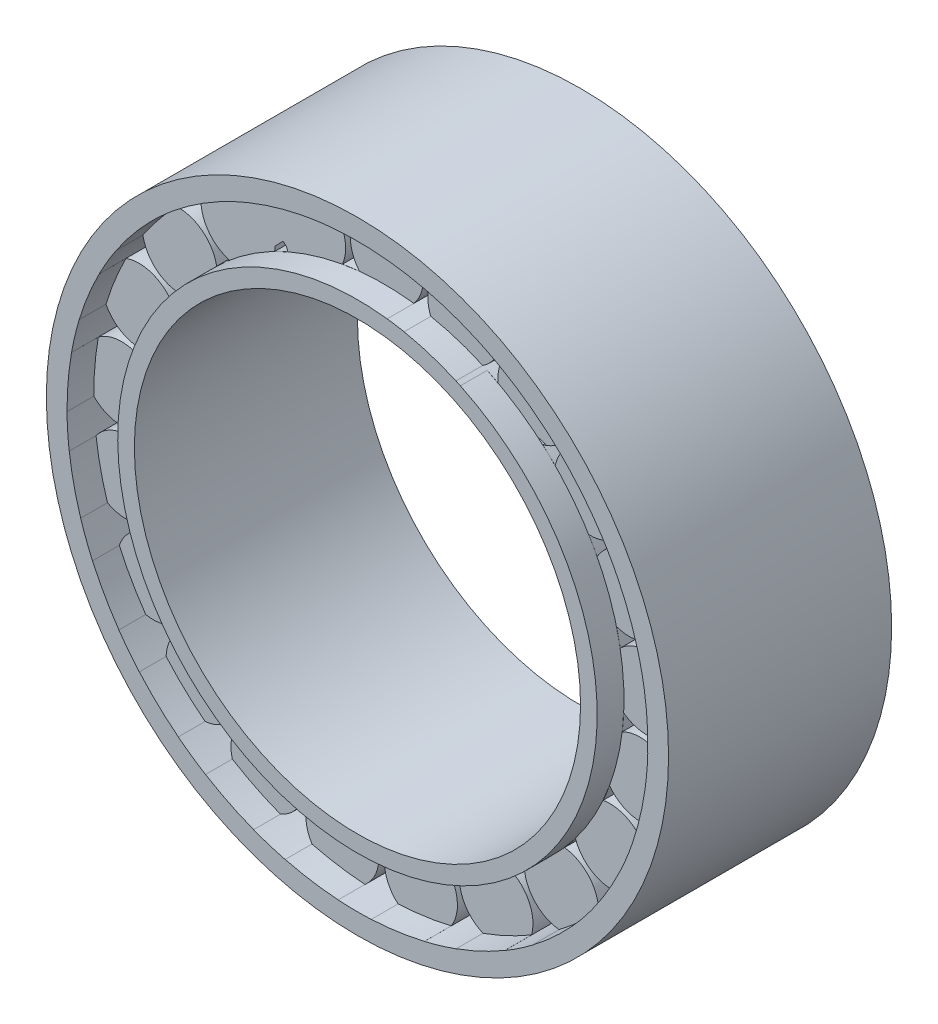
SolidWorks part; units mm, degrees
ref_plane "Front" through (0, 0, 0) normal (0, 0, 1) x (1, 0, 0)
ref_plane "Top" through (0, 0, 0) normal (0, 1, 0) x (1, 0, 0)
ref_plane "Right" through (0, 0, 0) normal (1, 0, 0) x (0, 0, -1)
sketch "Sketch1" plane through (0, 0, 0) normal (0, 0, 1) x (1, 0, 0)
  line L0 (0, 0) -> (0, 20.9407) construction
  circle A1 centre (0, 0) radius 17.7101
  circle A2 centre (0, 0) radius 12.7
  arc A3 (1.6898, 13.5424) -> (1.6754, 16.4463) centre (0, 14.986) ccw
  arc A4 (5.607, 12.4424) -> (6.4492, 15.2216) centre (4.4178, 14.32) ccw
  arc A5 (6.4823, 12.0097) -> (5.607, 12.4424) centre (0.0006, -0.0002) ccw
  arc A6 (8.1492, 14.3835) -> (6.4823, 12.0097) centre (8.694, 12.2288) ccw
  arc A7 (8.1492, 14.3835) -> (6.4492, 15.2216) centre (0.0006, -0.0002) ccw
  arc A8 (2.6538, 13.3869) -> (1.6898, 13.5424) centre (0, 0) ccw
  arc A9 (3.5469, 16.1465) -> (2.6538, 13.3869) centre (4.7026, 14.2481) ccw
  arc A10 (3.5469, 16.1465) -> (1.6754, 16.4463) centre (0, 0) ccw
  arc A11 (9.026, 10.2368) -> (10.6499, 12.6443) centre (8.443, 12.3814) ccw
  arc A12 (9.7349, 9.5653) -> (9.026, 10.2368) centre (0.0011, -0.0006) ccw
  arc A13 (12.0273, 11.3423) -> (9.7349, 9.5653) centre (11.9129, 9.1227) ccw
  arc A14 (12.0273, 11.3423) -> (10.6499, 12.6443) centre (0.0011, -0.0006) ccw
  arc A15 (11.6429, 7.1213) -> (13.9044, 8.9432) centre (11.718, 9.3425) ccw
  arc A16 (12.1224, 6.2707) -> (11.6429, 7.1213) centre (0.0015, -0.0011) ccw
  arc A17 (14.8368, 7.293) -> (12.1224, 6.2707) centre (14.0732, 5.2058) ccw
  arc A18 (14.8368, 7.293) -> (13.9044, 8.9432) centre (0.0015, -0.0011) ccw
  arc A19 (13.2253, 3.3729) -> (15.9233, 4.4473) centre (13.9518, 5.4733) ccw
  arc A20 (13.4328, 2.4188) -> (13.2253, 3.3729) centre (0.0017, -0.0017) ccw
  arc A21 (16.3279, 2.5956) -> (13.4328, 2.4188) centre (14.983, 0.8262) ccw
  arc A22 (16.3279, 2.5956) -> (15.9233, 4.4473) centre (0.0017, -0.0017) ccw
  arc A23 (13.6325, -0.6754) -> (16.5273, -0.444) centre (14.9459, 1.1176) ccw
  arc A24 (13.5495, -1.6483) -> (13.6325, -0.6754) centre (0.0018, -0.0023) ccw
  arc A25 (16.3682, -2.3326) -> (13.5495, -1.6483) centre (14.5615, -3.627) ccw
  arc A26 (16.3682, -2.3326) -> (16.5273, -0.444) centre (0.0018, -0.0023) ccw
  arc A27 (12.8284, -4.6638) -> (15.6628, -5.296) centre (14.6119, -3.3376) ccw
  arc A28 (12.4623, -5.569) -> (12.8284, -4.6638) centre (0.0016, -0.0029) ccw
  arc A29 (14.954, -7.0538) -> (12.4623, -5.569) centre (12.8461, -7.7581) ccw
  arc A30 (14.954, -7.0538) -> (15.6628, -5.296) centre (0.0016, -0.0029) ccw
  arc A31 (10.8844, -8.2381) -> (13.4065, -9.6776) centre (12.9795, -7.4965) ccw
  arc A32 (10.2678, -8.9951) -> (10.8844, -8.2381) centre (0.0013, -0.0035) ccw
  arc A33 (12.2111, -11.1484) -> (10.2678, -8.9951) centre (9.9892, -11.2001) ccw
  arc A34 (12.2111, -11.1484) -> (13.4065, -9.6776) centre (0.0013, -0.0035) ccw
  arc A35 (7.9732, -11.0805) -> (9.959, -13.1995) centre (10.1939, -10.9894) ccw
  arc A36 (7.1608, -11.6222) -> (7.9732, -11.0805) centre (0.0008, -0.0039) ccw
  arc A37 (8.3832, -14.2526) -> (7.1608, -11.6222) centre (6.2447, -13.6471) ccw
  arc A38 (8.3832, -14.2526) -> (9.959, -13.1995) centre (0.0008, -0.0039) ccw
  arc A39 (4.3536, -12.9386) -> (5.6266, -15.5487) centre (6.5024, -13.5061) ccw
  arc A40 (3.4176, -13.2167) -> (4.3536, -12.9386) centre (0.0002, -0.0042) ccw
  arc A41 (3.8103, -16.0906) -> (3.4176, -13.2167) centre (1.9453, -14.8817) ccw
  arc A42 (3.8103, -16.0906) -> (5.6266, -15.5487) centre (0.0002, -0.0042) ccw
  arc A43 (0.3471, -13.6472) -> (0.7941, -16.5166) centre (2.2331, -14.8229) ccw
  arc A44 (-0.6293, -13.6371) -> (0.3471, -13.6472) centre (-0.0004, -0.0042) ccw
  arc A45 (-1.1011, -16.499) -> (-0.6293, -13.6371) centre (-2.5269, -14.7941) ccw
  arc A46 (-1.1011, -16.499) -> (0.7941, -16.5166) centre (-0.0004, -0.0042) ccw
  arc A47 (-3.6903, -13.1434) -> (-4.1089, -16.0171) centre (-2.2346, -14.8228) ccw
  arc A48 (-4.6204, -12.846) -> (-3.6903, -13.1434) centre (-0.001, -0.0041) ccw
  arc A49 (-5.9148, -15.4416) -> (-4.6204, -12.846) centre (-6.7747, -13.3922) ccw
  arc A50 (-5.9148, -15.4416) -> (-4.1089, -16.0171) centre (-0.001, -0.0041) ccw
  arc A51 (-7.3999, -11.4719) -> (-8.6469, -14.0946) centre (-6.5038, -13.5058) ccw
  arc A52 (-8.2009, -10.9136) -> (-7.3999, -11.4719) centre (-0.0016, -0.0038) ccw
  arc A53 (-10.2029, -13.0124) -> (-8.2009, -10.9136) centre (-10.4205, -10.8006) ccw
  arc A54 (-10.2029, -13.0124) -> (-8.6469, -14.0946) centre (-0.0016, -0.0038) ccw
  arc A55 (-10.4519, -8.7813) -> (-12.4166, -10.9199) centre (-10.1951, -10.9889) ccw
  arc A56 (-11.0528, -8.0116) -> (-10.4519, -8.7813) centre (-0.0021, -0.0034) ccw
  arc A57 (-13.5845, -9.4271) -> (-11.0528, -8.0116) centre (-13.1405, -7.2494) ccw
  arc A58 (-13.5845, -9.4271) -> (-12.4166, -10.9199) centre (-0.0021, -0.0034) ccw
  arc A59 (-12.5753, -5.3106) -> (-15.083, -6.7751) centre (-12.9806, -7.4958) ccw
  arc A60 (-12.9226, -4.398) -> (-12.5753, -5.3106) centre (-0.0024, -0.0028) ccw
  arc A61 (-15.7591, -5.0044) -> (-12.9226, -4.398) centre (-14.6929, -3.0543) ccw
  arc A62 (-15.7591, -5.0044) -> (-15.083, -6.7751) centre (-0.0024, -0.0028) ccw
  arc A63 (-13.5813, -1.3683) -> (-16.4093, -2.0285) centre (-14.6128, -3.3369) ccw
  arc A64 (-13.6443, -0.3938) -> (-13.5813, -1.3683) centre (-0.0025, -0.0022) ccw
  arc A65 (-16.5334, -0.1372) -> (-13.6443, -0.3938) centre (-14.9398, 1.412) ccw
  arc A66 (-16.5334, -0.1372) -> (-16.4093, -2.0285) centre (-0.0025, -0.0022) ccw
  arc A67 (-13.3806, 2.6955) -> (-16.2776, 2.8981) centre (-14.9465, 1.1183) ccw
  arc A68 (-13.1536, 3.6452) -> (-13.3806, 2.6955) centre (-0.0024, -0.0016) ccw
  arc A69 (-15.8387, 4.742) -> (-13.1536, 3.6452) centre (-13.8593, 5.7526) ccw
  arc A70 (-15.8387, 4.742) -> (-16.2776, 2.8981) centre (-0.0024, -0.0016) ccw
  arc A71 (-11.9911, 6.5196) -> (-14.6996, 7.5671) centre (-13.9523, 5.474) ccw
  arc A72 (-11.4941, 7.3601) -> (-11.9911, 6.5196) centre (-0.0022, -0.001) ccw
  arc A73 (-13.7367, 9.1997) -> (-11.4941, 7.3601) centre (-11.5473, 9.582) ccw
  arc A74 (-13.7367, 9.1997) -> (-14.6996, 7.5671) centre (-0.0022, -0.001) ccw
  arc A75 (-9.5361, 9.7641) -> (-11.8155, 11.5635) centre (-11.7183, 9.3431) ccw
  arc A76 (-8.8135, 10.4209) -> (-9.5361, 9.7641) centre (-0.0018, -0.0005) ccw
  arc A77 (-10.4142, 12.8397) -> (-8.8135, 10.4209) centre (-8.2094, 12.5597) ccw
  arc A78 (-10.4142, 12.8397) -> (-11.8155, 11.5635) centre (-0.0018, -0.0005) ccw
  arc A79 (-6.2338, 12.141) -> (-7.8815, 14.5322) centre (-8.4432, 12.3819) ccw
  arc A80 (-5.3497, 12.5555) -> (-6.2338, 12.141) centre (-0.0012, -0.0002) ccw
  arc A81 (-6.1663, 15.3387) -> (-5.3497, 12.5555) centre (-4.142, 14.4213) ccw
  arc A82 (-6.1663, 15.3387) -> (-7.8815, 14.5322) centre (-0.0012, -0.0002) ccw
  arc A83 (-2.3776, 13.4388) -> (-3.2473, 16.2095) centre (-4.4178, 14.3202) ccw
  arc A84 (-1.4106, 13.5744) -> (-2.3776, 13.4388) centre (-0.0006, 0) ccw
  arc A85 (-1.3706, 16.4746) -> (-1.4106, 13.5744) centre (0.2933, 15.0013) ccw
  arc A86 (-1.3706, 16.4746) -> (-3.2473, 16.2095) centre (-0.0006, 0) ccw
  dimension "D1" = 25.4
  dimension "D2" = 4.445
  dimension "D3" = 14.986
extrude "Base-Extrude" add sketch "Sketch1" against normal blind 6.35
sketch "Sketch2" plane through (0, 0, 0) normal (0, 0, 1) x (1, 0, 0)
  circle A0 centre (0, 0) radius 13.6475
  circle A1 centre (0, 0) radius 16.5315
extrude "Cut-Extrude1" cut sketch "Sketch2" against normal blind 1.524
mirror "Mirror All1" about plane through (0, 0, -6.35) normal (0, 0, 1) of bodies 102
